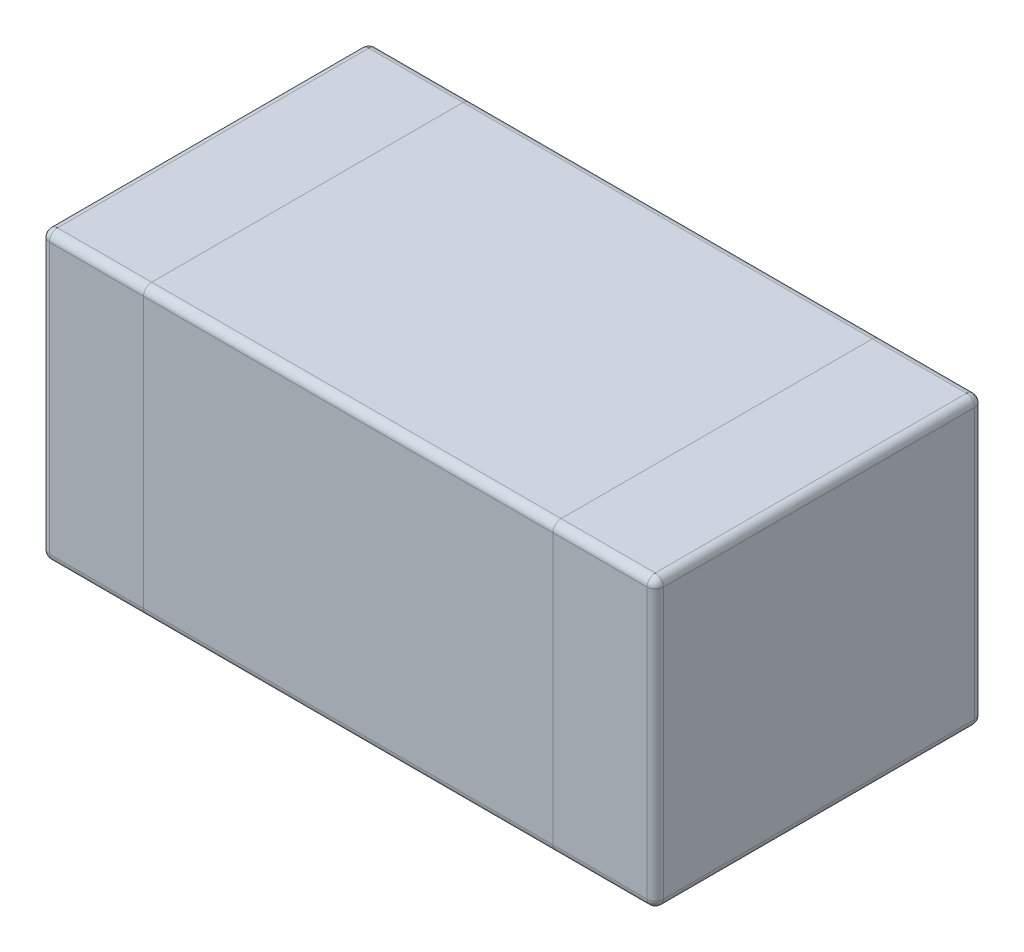
SolidWorks part; units mm, degrees
ref_plane "Front Plane" through (0, 0, 0) normal (0, 0, 1) x (1, 0, 0)
ref_plane "Top Plane" through (0, 0, 0) normal (0, 1, 0) x (1, 0, 0)
ref_plane "Right Plane" through (0, 0, 0) normal (1, 0, 0) x (0, 0, -1)
sketch "Sketch1" plane through (0, 0, 0) normal (0, 1, 0) x (1, 0, 0)
  line L1 (-0.73, -0.4) -> (0.73, -0.4)
  line L2 (-0.75, -0.38) -> (-0.75, 0.38)
  line L3 (-0.73, 0.4) -> (0.73, 0.4)
  line L4 (0.75, -0.38) -> (0.75, 0.38)
  line L5 (-0.75, -0.4) -> (0.75, 0.4) construction
  line L6 (-0.75, 0.4) -> (0.75, -0.4) construction
  arc A4 (-0.75, -0.38) -> (-0.73, -0.4) centre (-0.73, -0.38) ccw
  arc A5 (0.73, -0.4) -> (0.75, -0.38) centre (0.73, -0.38) ccw
  arc A6 (0.75, 0.38) -> (0.73, 0.4) centre (0.73, 0.38) ccw
  arc A7 (-0.73, 0.4) -> (-0.75, 0.38) centre (-0.73, 0.38) ccw
  point P0 (0, 0)
  dimension "D4" = 0.02
  dimension "D1" = 1.5
  dimension "D2" = 0.8
extrude "Boss-Extrude1" add sketch "Sketch1" along normal mid plane 0.7
sketch "Sketch3" plane through (0, 0.35, 0) normal (0, 1, 0) x (1, 0, 0)
  line L0 (-0.5, 0) -> (0.5, 0) construction
  line L1 (-0.5, -0.5133) -> (-0.5, 0.5133)
  line L2 (0.5, -0.5133) -> (0.5, 0.5133)
  line L3 (0, -0.145) -> (0, 0.145) construction
  line L6 (-0.5, -0.145) -> (0.5, -0.145) construction
  point P4 (0, 0)
  point P8 (-0.5, 0)
  point P11 (0.5, 0)
  point P14 (0, 0)
  point P17 (0, -0.145)
  dimension "D1" = 1
  dimension "D2" = 0.29
sketch "Sketch4" plane through (0, 0, 0.4) normal (0, 0, 1) x (1, 0, 0)
  line L0 (-0.5, 0.35) -> (-0.5, -0.5946)
  line L1 (0.5, 0.35) -> (0.5, -0.5946)
sketch "Sketch5" plane through (0, 0, -0.4) normal (0, 0, -1) x (-1, 0, 0)
  line L0 (-0.5, 0.35) -> (-0.5, -0.5946) construction
  line L1 (-0.5, 0.35) -> (-0.5, -0.5946)
  line L2 (0.5, 0.35) -> (0.5, -0.5946) construction
  line L3 (0.5, 0.35) -> (0.5, -0.5946)
sketch "Sketch6" plane through (0, -0.35, 0) normal (0, -1, 0) x (1, 0, 0)
  line L0 (0.5, 0.5133) -> (0.5, -0.5133) construction
  line L1 (-0.5, 0.5133) -> (-0.5, -0.5133) construction
  line L2 (0.5, 0.5133) -> (0.5, -0.5133)
  line L3 (-0.5, 0.5133) -> (-0.5, -0.5133)
split line "Split Line2"
split line "Split Line3"
split line "Split Line4"
split line "Split Line5"
fillet "Fillet2" radius 0.02 24 edges at (0.615, -0.35, 0.4) (-0.615, -0.35, 0.4) (0, -0.35, 0.4) (-0.7441, -0.35, 0.3941) (-0.75, -0.35, 0) (-0.7441, -0.35, -0.3941) (-0.615, -0.35, -0.4) (0.615, -0.35, -0.4) (0, -0.35, -0.4) (0.7441, -0.35, -0.3941) (0.75, -0.35, 0) (0.7441, -0.35, 0.3941) (-0.615, 0.35, -0.4) (0, 0.35, -0.4) (0.615, 0.35, -0.4) (0.7441, 0.35, -0.3941) (0.75, 0.35, 0) (0.7441, 0.35, 0.3941) (-0.615, 0.35, 0.4) (0, 0.35, 0.4) (0.615, 0.35, 0.4) (-0.7441, 0.35, 0.3941) (-0.75, 0.35, 0) (-0.7441, 0.35, -0.3941)
